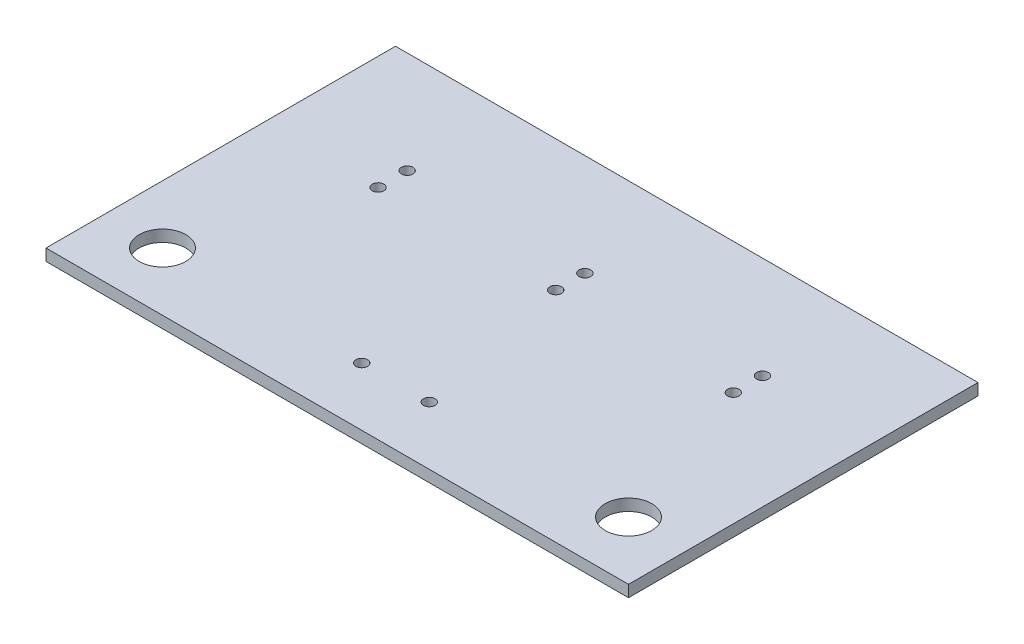
SolidWorks part; units mm, degrees
ref_plane "Front Plane" through (0, 0, 0) normal (0, 0, 1) x (1, 0, 0)
ref_plane "Top Plane" through (0, 0, 0) normal (0, 1, 0) x (1, 0, 0)
ref_plane "Right Plane" through (0, 0, 0) normal (1, 0, 0) x (0, 0, -1)
sketch "Sketch1" plane through (0, 0, 0) normal (0, 1, 0) x (1, 0, 0)
  line L1 (0, 0) -> (50, 0)
  line L2 (0, 0) -> (0, 30)
  line L3 (0, 30) -> (50, 30)
  line L4 (50, 0) -> (50, 30)
  dimension "D1" = 30
  dimension "D2" = 50
extrude "Boss-Extrude1" add sketch "Sketch1" along normal blind 1
sketch "Sketch2" plane through (0, 1, 0) normal (0, 1, 0) x (1, 0, 0)
  line L0 (25, 0) -> (25, 30) construction
  line L1 (0, 0) -> (50, 0) construction
  line L2 (50, 30) -> (0, 30) construction
  line L3 (22.1, 5) -> (27.9, 5) construction
  line L4 (0, 20) -> (50, 20) construction
  line L5 (0, 30) -> (0, 0) construction
  line L6 (50, 0) -> (50, 30) construction
  line L7 (9.75, 21.25) -> (40.25, 21.25) construction
  line L8 (9.75, 18.75) -> (40.25, 18.75) construction
  line L9 (9.75, 18.75) -> (9.75, 21.25) construction
  line L10 (40.25, 18.75) -> (40.25, 21.25) construction
  line L11 (0, 0) -> (50, 0) construction
  line L12 (0, 30) -> (0, 0) construction
  circle A0 centre (22.1, 5) radius 0.5
  circle A1 centre (27.9, 5) radius 0.5
  circle A2 centre (9.75, 18.75) radius 0.5
  circle A3 centre (9.75, 21.25) radius 0.5
  circle A4 centre (25, 18.75) radius 0.5
  circle A5 centre (25, 21.25) radius 0.5
  circle A6 centre (40.25, 18.75) radius 0.5
  circle A7 centre (40.25, 21.25) radius 0.5
  circle A8 centre (45, 5) radius 2
  circle A9 centre (5, 5) radius 2
  point P10 (25, 5)
  dimension "D3" = 1
  dimension "D8" = 15.25
  dimension "D9" = 4
  dimension "D10" = 4
  dimension "D1" = 5
  dimension "D2" = 10
  dimension "D4" = 5.8
  dimension "D5" = 2.5
  dimension "D6" = 1.25
  dimension "D7" = 15.25
  dimension "D11" = 5
  dimension "D12" = 5
  dimension "D13" = 5
  dimension "D14" = 5
extrude "Cut-Extrude1" cut sketch "Sketch2" against normal blind 1
